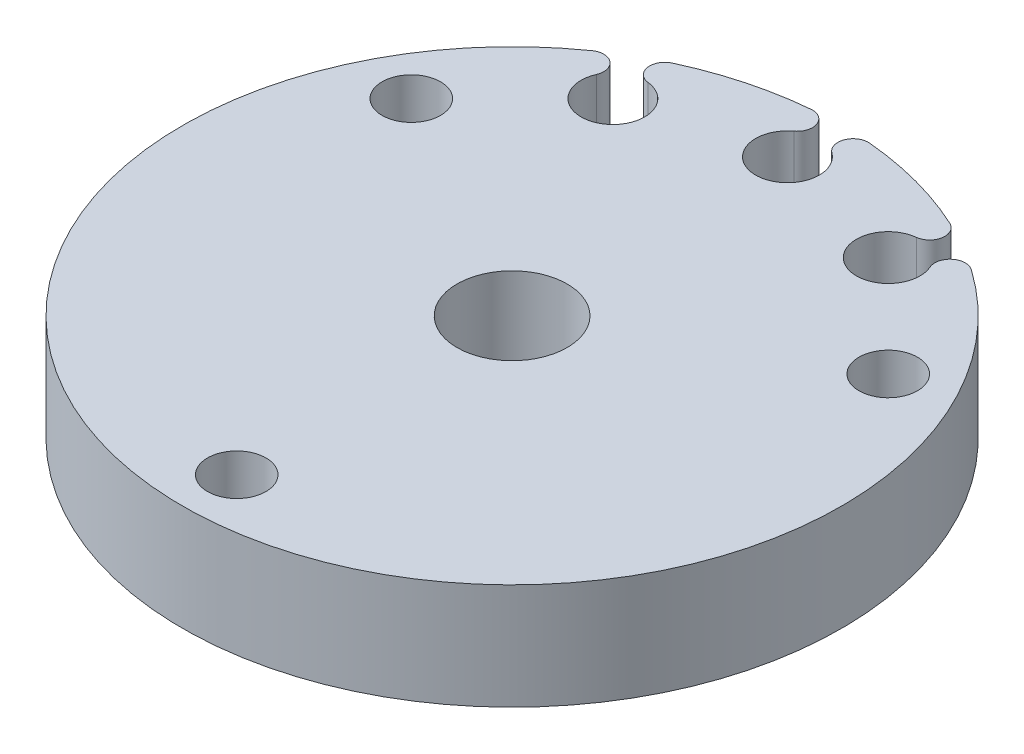
SolidWorks part; units mm, degrees
material "Cedar"
ref_plane "Front Plane" through (0, 0, 0) normal (0, 0, 1) x (1, 0, 0)
ref_plane "Top Plane" through (0, 0, 0) normal (0, 1, 0) x (1, 0, 0)
ref_plane "Right Plane" through (0, 0, 0) normal (1, 0, 0) x (0, 0, -1)
sketch "Sketch1" plane through (0, 0, 0) normal (0, 1, 0) x (1, 0, 0)
  line L0 (0, 16.5) -> (-14.2894, 8.25) construction
  line L1 (-14.2894, 8.25) -> (-14.2894, -8.25) construction
  circle A0 centre (0, 0) radius 19.75
  circle A1 centre (0, 0) radius 16.5 construction
  circle A2 centre (0, 0) radius 3.302
  circle A3 centre (0, 16.5) radius 1.75 construction
  circle A4 centre (-14.2894, 8.25) radius 1.75
  circle A5 centre (-14.2894, -8.25) radius 2.58 construction
  circle A6 centre (0, -16.5) radius 1.75
  circle A7 centre (14.2894, -8.25) radius 2.58 construction
  circle A8 centre (14.2894, 8.25) radius 1.75
  dimension "D1" = 39.5
  dimension "D2" = 33
  dimension "D3" = 6.604
  dimension "D4" = 3.5
  dimension "D5" = 5.16
extrude "Boss-Extrude1" add sketch "Sketch1" along normal blind 6.35
sketch "Sketch2" plane through (0, 6.35, 0) normal (0, 1, 0) x (1, 0, 0)
  line L0 (0, 0) -> (0, 11.1551) construction
  line L1 (7.1447, 12.375) -> (0, 0) construction
  line L2 (0, 0) -> (3.7596, 6.5118) construction
  arc A0 (8.0362, 16.1824) -> (9.9963, 15.0507) centre (8.25, 14.2894) ccw
  circle A1 centre (0, 0) radius 19.75 construction
  arc A2 (11.3546, 16.1597) -> (8.3174, 17.9132) centre (0, 0) ccw
  arc A3 (11.3546, 16.1597) -> (9.9963, 15.0507) centre (10.831, 15.4146) ccw
  arc A4 (8.3174, 17.9132) -> (8.0362, 16.1824) centre (7.9339, 17.0873) cw
  circle A5 centre (7.7822, 13.2861) radius 0.5207 construction
  circle A6 centre (7.4242, 14.8077) radius 0.6604 construction
  circle A7 centre (8.9696, 15.2328) radius 0.6604 construction
  circle A8 centre (9.1903, 13.6875) radius 0.5207 construction
  dimension "D2" = 3.81
  dimension "D5" = 1.0414
  dimension "D3" = 1.524
  dimension "D4" = 1.3208
  dimension "D1" = 16.5
  dimension "D6" = 30
extrude "Cut-Extrude1" cut sketch "Sketch2" against normal through all
pattern_circular "CirPattern1" count 3 every 30 about axis through (0, 0, 0) along (0, 1, 0) of "Cut-Extrude1"
